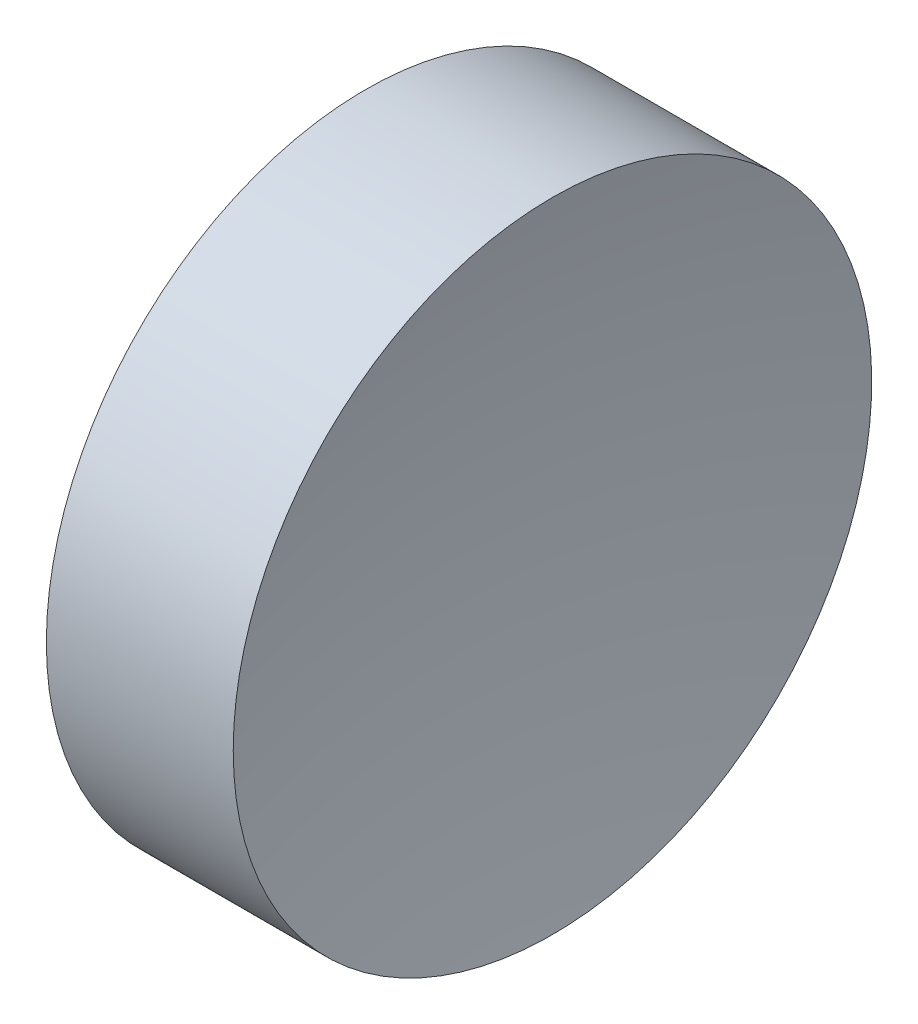
SolidWorks part; units mm, degrees
ref_plane "前视基准面" through (0, 0, 0) normal (0, 0, 1) x (1, 0, 0)
ref_plane "上视基准面" through (0, 0, 0) normal (0, 1, 0) x (1, 0, 0)
ref_plane "右视基准面" through (0, 0, 0) normal (1, 0, 0) x (0, 0, -1)
sketch "草图1" plane through (0, 0, 0) normal (0, 0, 1) x (1, 0, 0)
  line L0 (54.4926, 34.689) -> (66.3882, 34.689) construction
  line L1 (57.5463, 34.689) -> (57.5463, 40.939)
  line L2 (57.5463, 40.939) -> (61.2046, 40.939)
  line L3 (60.5463, 34.689) -> (57.5463, 34.689)
  arc A0 (61.2046, 40.939) -> (60.5463, 34.689) centre (90.5463, 34.689) ccw
  dimension "D1" = 3.6583
revolve "旋转1" add sketch "草图1" angle 360 about L0
